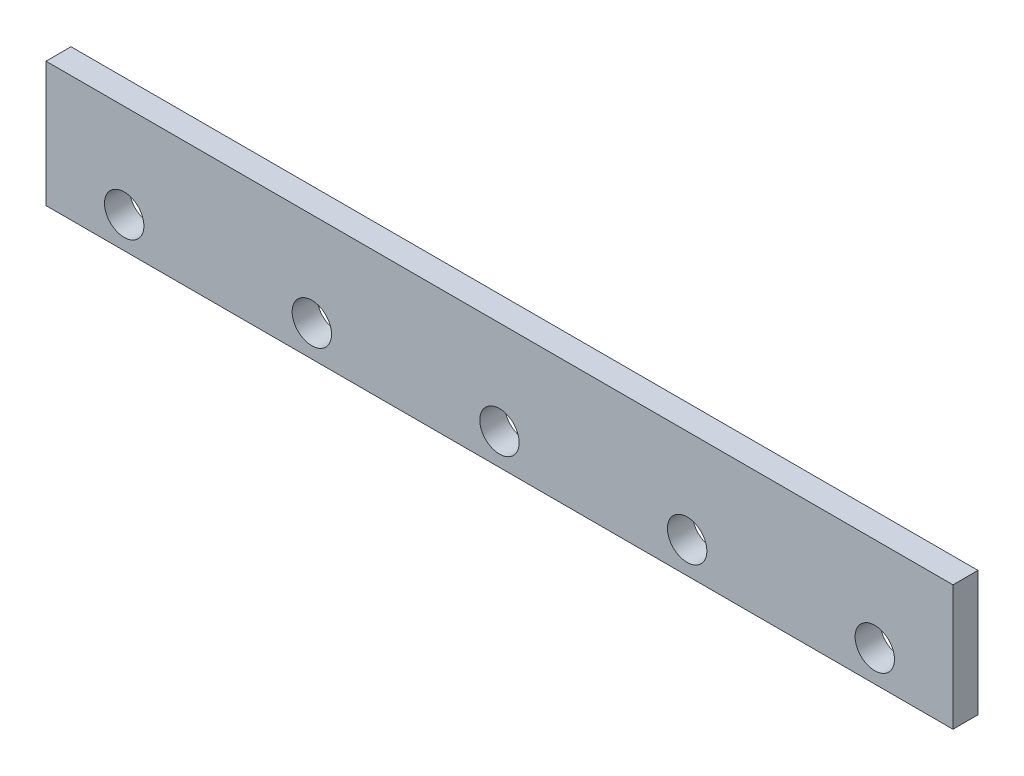
SolidWorks part; units mm, degrees
ref_plane "Front Plane" through (0, 0, 0) normal (0, 0, 1) x (1, 0, 0)
ref_plane "Top Plane" through (0, 0, 0) normal (0, 1, 0) x (1, 0, 0)
ref_plane "Right Plane" through (0, 0, 0) normal (1, 0, 0) x (0, 0, -1)
sketch "Sketch1" plane through (0, 0, 0) normal (0, 0, 1) x (1, 0, 0)
  line L1 (0, 0) -> (580, 0)
  line L2 (0, 0) -> (0, 80)
  line L3 (0, 80) -> (580, 80)
  line L4 (580, 0) -> (580, 80)
  dimension "D1" = 580
  dimension "D2" = 80
extrude "Boss-Extrude1" add sketch "Sketch1" along normal blind 16
sketch "Sketch2" plane through (0, 0, 16) normal (0, 0, 1) x (1, 0, 0)
  line L0 (0, 0) -> (580, 0) construction
  line L1 (0, 80) -> (0, 0) construction
  circle A0 centre (50, 20) radius 12.6
  dimension "D1" = 25.2
  dimension "D2" = 20
  dimension "D3" = 50
extrude "Cut-Extrude1" cut sketch "Sketch2" against normal blind 16
sketch "Sketch4" plane through (0, 0, 16) normal (0, 0, 1) x (1, 0, 0)
  line L0 (0, 0) -> (580, 0) construction
  line L1 (0, 80) -> (0, 0) construction
  circle A0 centre (170, 20) radius 12.6
  dimension "D1" = 25.2
  dimension "D2" = 20
  dimension "D3" = 170
extrude "Cut-Extrude2" cut sketch "Sketch4" against normal blind 16
sketch "Sketch5" plane through (0, 0, 16) normal (0, 0, 1) x (1, 0, 0)
  line L0 (0, 80) -> (0, 0) construction
  line L1 (0, 0) -> (580, 0) construction
  circle A0 centre (290, 20) radius 12.6
  circle A1 centre (410, 20) radius 12.6
  circle A2 centre (530, 20) radius 12.6
  point P10 (290, 0)
  dimension "D1" = 25.2
  dimension "D2" = 120
  dimension "D8" = 25.2
  dimension "D9" = 25.2
  dimension "D3" = 120
  dimension "D4" = 290
  dimension "D5" = 20
  dimension "D6" = 20
  dimension "D7" = 20
extrude "Cut-Extrude3" cut sketch "Sketch5" against normal blind 16
